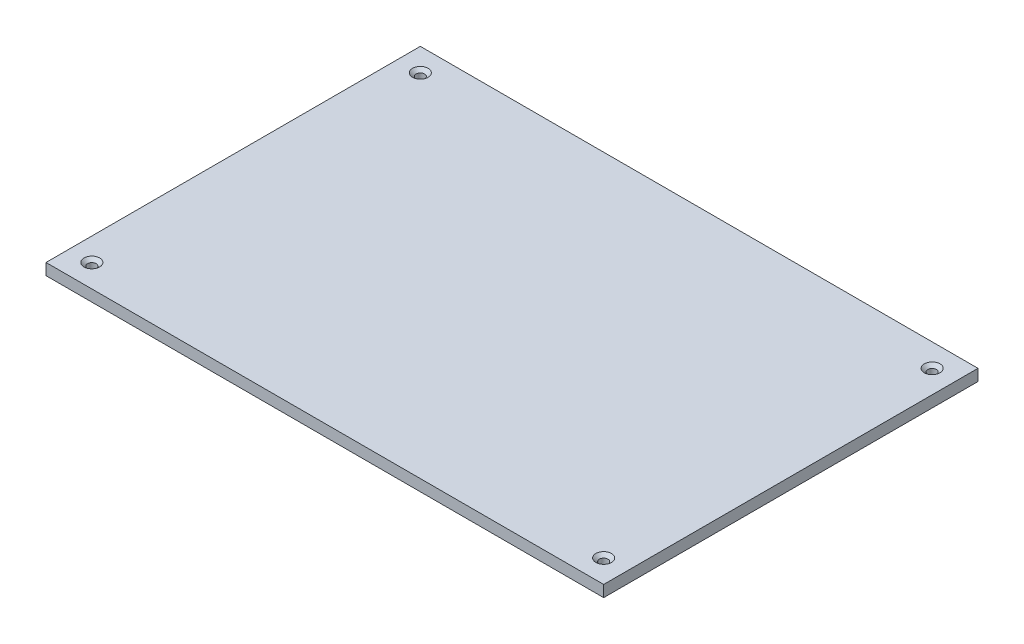
SolidWorks part; units mm, degrees
material "PC High Viscosity"
ref_plane "Front Plane" through (0, 0, 0) normal (0, 0, 1) x (1, 0, 0)
ref_plane "Top Plane" through (0, 0, 0) normal (0, 1, 0) x (1, 0, 0)
ref_plane "Right Plane" through (0, 0, 0) normal (1, 0, 0) x (0, 0, -1)
sketch "Sketch1" plane through (0, 0, 0) normal (0, 1, 0) x (1, 0, 0)
  line L1 (0, 0) -> (463.55, 0)
  line L2 (0, 0) -> (0, -311.15)
  line L3 (0, -311.15) -> (463.55, -311.15)
  line L4 (463.55, 0) -> (463.55, -311.15)
  dimension "D1" = 463.55
  dimension "D2" = 311.15
extrude "Boss-Extrude1" add sketch "Sketch1" along normal blind 9.525
sketch "Sketch2" plane through (0, 9.525, 0) normal (0, 1, 0) x (1, 0, 0)
  line L0 (463.55, 0) -> (0, 0) construction
  line L1 (463.55, -311.15) -> (463.55, 0) construction
  line L2 (231.775, 0) -> (231.775, -311.15) construction
  line L3 (0, -311.15) -> (463.55, -311.15) construction
  line L4 (0, -155.575) -> (463.55, -155.575) construction
  line L5 (0, 0) -> (0, -311.15) construction
  circle A0 centre (444.5, -19.05) radius 3.5719
  circle A1 centre (19.05, -19.05) radius 3.5719
  circle A2 centre (444.5, -292.1) radius 3.5719
  circle A3 centre (19.05, -292.1) radius 3.5719
  dimension "D1" = 7.1437
  dimension "D2" = 273.05
  dimension "D3" = 425.45
extrude "Cut-Extrude1" cut sketch "Sketch2" against normal up to surface (9.525 mm away) up to face at (231.775, 0, 155.575)
sketch "Sketch4" plane through (0, 9.525, 0) normal (0, 1, 0) x (1, 0, 0)
  line L0 (38.1, 0) -> (38.1, -311.15) construction
  line L1 (463.55, 0) -> (0, 0) construction
  line L2 (0, -311.15) -> (463.55, -311.15) construction
  line L3 (425.45, 0) -> (425.45, -311.15) construction
  line L4 (0, -38.1) -> (463.55, -38.1) construction
  line L5 (0, 0) -> (0, -311.15) construction
  line L6 (463.55, -311.15) -> (463.55, 0) construction
  line L7 (0, -273.05) -> (463.55, -273.05) construction
  point P16 (38.1, -155.575)
  point P17 (425.45, -155.575)
  dimension "D1" = 38.1
  dimension "D2" = 38.1
  dimension "D3" = 38.1
  dimension "D4" = 38.1
chamfer "Chamfer1" distance 2.921 angle 42 4 edges at (444.5, 9.525, 288.5281) (444.5, 9.525, 22.6219) (19.05, 9.525, 15.4781) (19.05, 9.525, 295.6719)
equation "\".115n\"=0.161"
